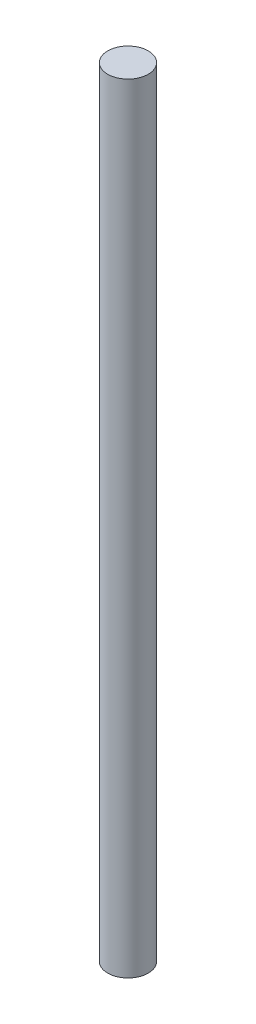
SolidWorks part; units mm, degrees
ref_plane "Front Plane" through (0, 0, 0) normal (0, 0, 1) x (1, 0, 0)
ref_plane "Top Plane" through (0, 0, 0) normal (0, 1, 0) x (1, 0, 0)
ref_plane "Right Plane" through (0, 0, 0) normal (1, 0, 0) x (0, 0, -1)
sketch "Sketch1" plane through (0, 0, 0) normal (0, 1, 0) x (1, 0, 0)
  circle A0 centre (0, 0) radius 3.9688
  dimension "D1" = 7.9375
extrude "Boss-Extrude1" add sketch "Sketch1" along normal blind 152.4
